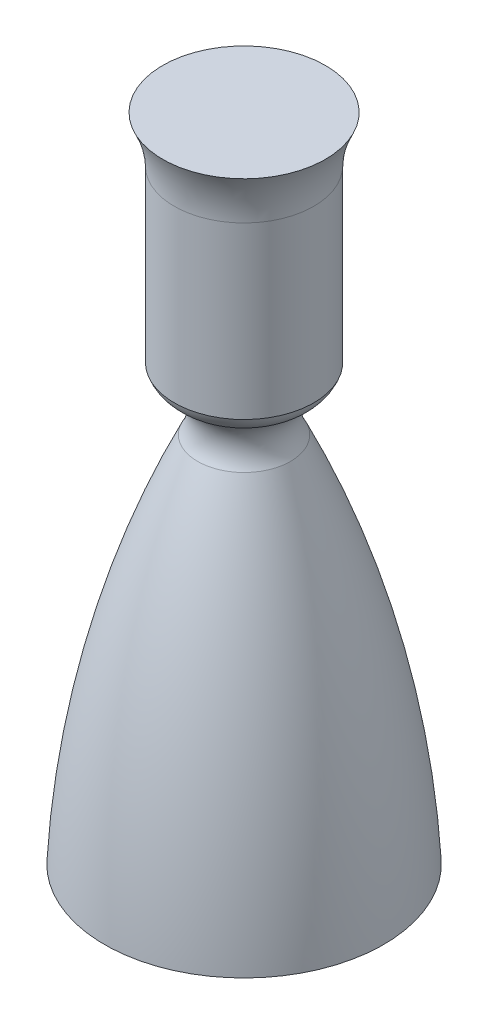
SolidWorks part; units mm, degrees
ref_plane "Front Plane" through (0, 0, 0) normal (0, 0, 1) x (1, 0, 0)
ref_plane "Top Plane" through (0, 0, 0) normal (0, 1, 0) x (1, 0, 0)
ref_plane "Right Plane" through (0, 0, 0) normal (1, 0, 0) x (0, 0, -1)
sketch "Sketch1" plane through (0, 0, 0) normal (0, 0, 1) x (1, 0, 0)
  line L0 (0, 0) -> (76.2, 0)
  line L1 (0, 0) -> (0, 355.6)
  line L2 (0, 203.2) -> (25.4, 203.2) construction
  line L3 (38.1, 237.222) -> (0, 237.222) construction
  line L4 (38.1, 237.222) -> (38.1, 330.2)
  line L5 (0, 355.6) -> (44.45, 355.6)
  arc A0 (25.4, 203.2) -> (76.2, 0) centre (-468.2775, -28.1694) cw
  arc A1 (25.4, 203.2) -> (28.1397, 226.6524) centre (40.8858, 213.2772) cw
  arc A2 (28.1397, 226.6524) -> (38.1, 237.222) centre (20.9845, 243.3729) ccw
  arc A3 (38.1, 330.2) -> (44.45, 355.6) centre (95.3946, 329.3701) cw
  dimension "D1" = 76.2
  dimension "D2" = 355.6
  dimension "D3" = 203.2
  dimension "D4" = 25.4
  dimension "D5" = 38.1
  dimension "D6" = 25.4
  dimension "D7" = 44.45
revolve "Revolve1" add sketch "Sketch1" angle 360 about L1
